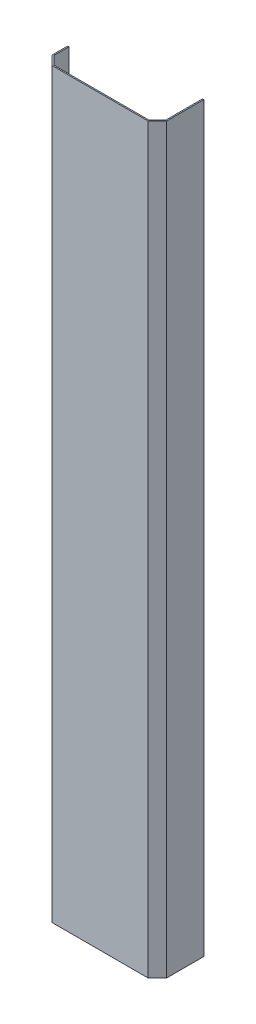
SolidWorks part; units mm, degrees
ref_plane "Front Plane" through (0, 0, 0) normal (0, 0, 1) x (1, 0, 0)
ref_plane "Top Plane" through (0, 0, 0) normal (0, 1, 0) x (1, 0, 0)
ref_plane "Right Plane" through (0, 0, 0) normal (1, 0, 0) x (0, 0, -1)
sketch "Sketch1" plane through (0, 0, 0) normal (0, 1, 0) x (1, 0, 0)
  line L0 (15.8284, 2) -> (2, 15.8284)
  line L1 (0, 0) -> (2, 0)
  line L2 (0, 15) -> (0, 40)
  line L3 (0, 40) -> (2, 40)
  line L4 (2, 15.8284) -> (2, 40)
  line L5 (0, 0) -> (2, 40) construction
  line L6 (0, 40) -> (2, 0) construction
  line L7 (15, 0) -> (170, 0)
  line L8 (0, 0) -> (0, 2)
  line L9 (15.8284, 2) -> (169.1716, 2)
  line L10 (185, 0) -> (185, 2)
  line L11 (0, 0) -> (185, 2) construction
  line L12 (0, 2) -> (185, 0) construction
  line L13 (185, 0) -> (183, 0)
  line L14 (185, 15) -> (185, 75)
  line L15 (185, 75) -> (183, 75)
  line L16 (183, 15.8284) -> (183, 75)
  line L17 (185, 0) -> (183, 75) construction
  line L18 (185, 75) -> (183, 0) construction
  line L19 (15, 0) -> (0, 15)
  line L21 (170, 0) -> (185, 15)
  line L22 (16.4142, 1.4142) -> (1.4142, 16.4142) construction
  line L25 (169.1716, 2) -> (183, 15.8284)
  point P4 (1, 20)
  point P9 (92.5, 1)
  point P13 (184, 37.5)
  point P16 (2, 2)
  point P21 (183, 2)
  dimension "D1" = 2
  dimension "D2" = 2
  dimension "D3" = 2
  dimension "D4" = 40
  dimension "D5" = 185
  dimension "D6" = 75
  dimension "D7" = 2
extrude "Boss-Extrude1" add sketch "Sketch1" along normal blind 1200 contours L7 L16 L9 L4
